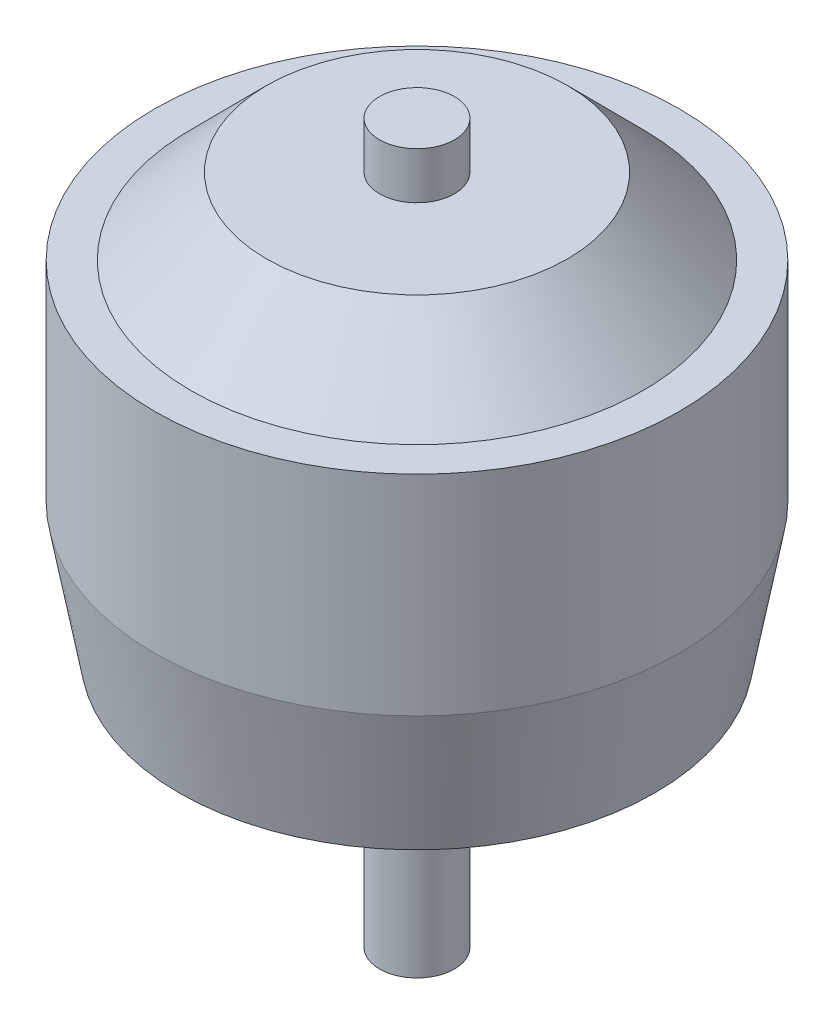
SolidWorks part; units mm, degrees
ref_plane "Front Plane" through (0, 0, 0) normal (0, 0, 1) x (1, 0, 0)
ref_plane "Top Plane" through (0, 0, 0) normal (0, 1, 0) x (1, 0, 0)
ref_plane "Right Plane" through (0, 0, 0) normal (1, 0, 0) x (0, 0, -1)
other "Bounding Box"
ref_plane "Default Plane" through (-8.9266, -12.7485, 0) normal (-0.1736, 0.9848, 0) x (0.9848, 0.1736, 0)
sketch "Sketch1" plane through (0, 0, 0) normal (1, 0, 0) x (0, 0, -1)
  line L0 (0, 0) -> (0, -1089.8708) construction
  line L1 (0, -16.8656) -> (-2.5, -16.8656)
  line L2 (-2.5, -16.8656) -> (-2.5, 0)
  line L3 (-2.5, 0) -> (-15.875, 0)
  line L4 (-15.875, 0) -> (-17.5006, 8.89)
  line L5 (-17.5006, 8.89) -> (-17.5006, 22.86)
  line L6 (-17.5006, 22.86) -> (-15.0876, 22.86)
  line L7 (-15.0876, 22.86) -> (-10.033, 27.94)
  line L8 (-10.033, 27.94) -> (-2.5, 27.94)
  line L9 (-2.5, 27.94) -> (-2.5, 31.0642)
  line L10 (-2.5, 31.0642) -> (0, 31.0642)
  line L11 (0, 31.0642) -> (0, -16.8656)
  dimension "D1" = 5
  dimension "D2" = 35.0012
  dimension "D3" = 27.94
  dimension "D4" = 47.9298
  dimension "D5" = 3.1242
  dimension "D6" = 8.89
  dimension "D7" = 31.75
  dimension "D8" = 2.413
  dimension "D9" = 20.066
  dimension "D10" = 22.86
revolve "Revolve1" add sketch "Sketch1" angle 360 about L0
